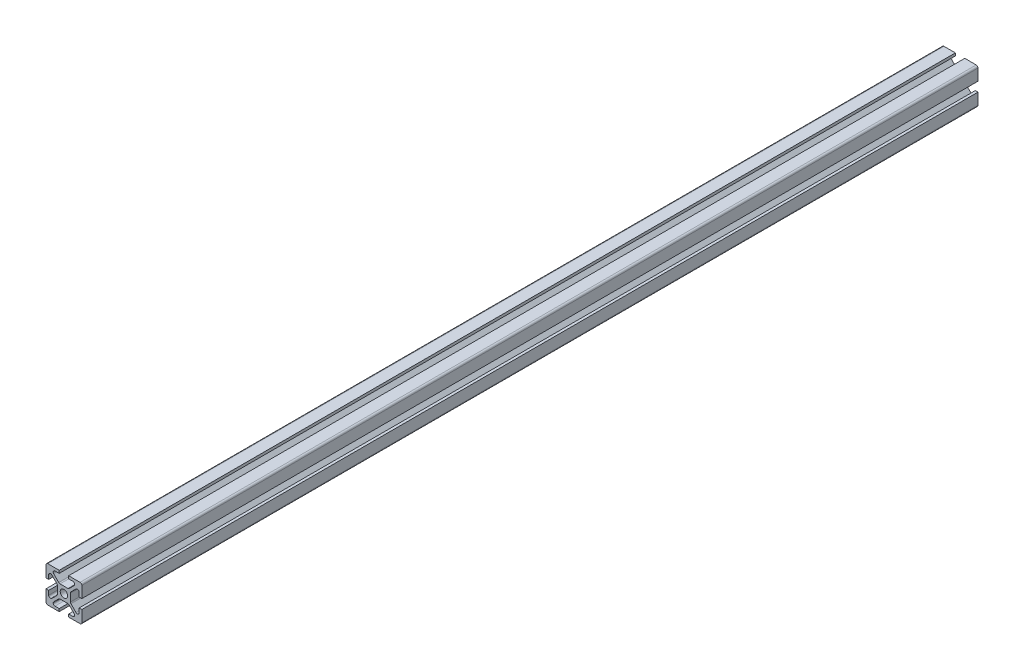
SolidWorks part; units mm, degrees
material "6061-T6 (SS)"
ref_plane "Front Plane" through (0, 0, 0) normal (0, 0, 1) x (1, 0, 0)
ref_plane "Top Plane" through (0, 0, 0) normal (0, 1, 0) x (1, 0, 0)
ref_plane "Right Plane" through (0, 0, 0) normal (1, 0, 0) x (0, 0, -1)
sketch "Sketch1" plane through (0, 0, 0) normal (0, 0, 1) x (1, 0, 0)
  line L0 (-10, 10) -> (10, -10) construction
  line L1 (-9, 10) -> (9, 10)
  line L2 (-10, 9) -> (-10, -9)
  line L3 (-9, -10) -> (9, -10)
  line L4 (10, 9) -> (10, -9)
  circle A0 centre (0, 0) radius 2.06
  arc A1 (-10, -9) -> (-9, -10) centre (-9, -9) ccw
  arc A2 (9, 10) -> (10, 9) centre (9, 9) cw
  arc A3 (10, -9) -> (9, -10) centre (9, -9) cw
  arc A4 (-9, 10) -> (-10, 9) centre (-9, 9) ccw
  dimension "D2" = 4.12
  dimension "D3" = 1
  dimension "D1" = 20
extrude "Boss-Extrude1" add sketch "Sketch1" along normal mid plane 500
sketch "Sketch2" plane through (0, 0, -250) normal (0, 0, -1) x (-1, 0, 0)
  line L0 (-10, 2.63) -> (-8.5, 2.63)
  line L1 (-10, -9) -> (-10, 9) construction
  line L2 (-8.5, 2.63) -> (-8.5, 4.995)
  line L3 (-6.7628, 5.7021) -> (-3.9479, 2.8872)
  line L4 (-3.655, 2.1801) -> (-3.655, -2.1801)
  line L5 (-3.9479, -2.8872) -> (-6.7628, -5.7021)
  line L6 (-8.5, -4.995) -> (-8.5, -2.63)
  line L7 (-8.5, -2.63) -> (-10, -2.63)
  line L8 (-10, -2.63) -> (-10, 2.63)
  line L9 (-10, 0) -> (-3.655, 0) construction
  line L10 (-3.655, 0) -> (0, 0) construction
  line L11 (-9, 9) -> (9, -9) construction
  line L12 (-9, -9) -> (9, 9) construction
  line L13 (-7.5, 5.995) -> (-7.4699, 5.995)
  line L14 (-7.5, -5.995) -> (-7.4699, -5.995)
  arc A0 (-7.5, 5.995) -> (-8.5, 4.995) centre (-7.5, 4.995) ccw
  arc A1 (-7.4699, 5.995) -> (-6.7628, 5.7021) centre (-7.4699, 4.995) cw
  arc A2 (-3.9479, 2.8872) -> (-3.655, 2.1801) centre (-4.655, 2.1801) cw
  arc A3 (-3.655, -2.1801) -> (-3.9479, -2.8872) centre (-4.655, -2.1801) cw
  arc A4 (-7.4699, -5.995) -> (-6.7628, -5.7021) centre (-7.4699, -4.995) ccw
  arc A5 (-7.5, -5.995) -> (-8.5, -4.995) centre (-7.5, -4.995) cw
  dimension "D6" = 1
  dimension "D1" = 3.655
  dimension "D2" = 0.75
  dimension "D3" = 1.5
  dimension "D4" = 5.26
  dimension "D5" = 11.99
extrude "Cut-Extrude1" cut sketch "Sketch2" against normal through all
pattern_circular "CirPattern1" count 4 over 360 about axis through (0, 0, 0) along (0, 0, 1) of "Cut-Extrude1"
